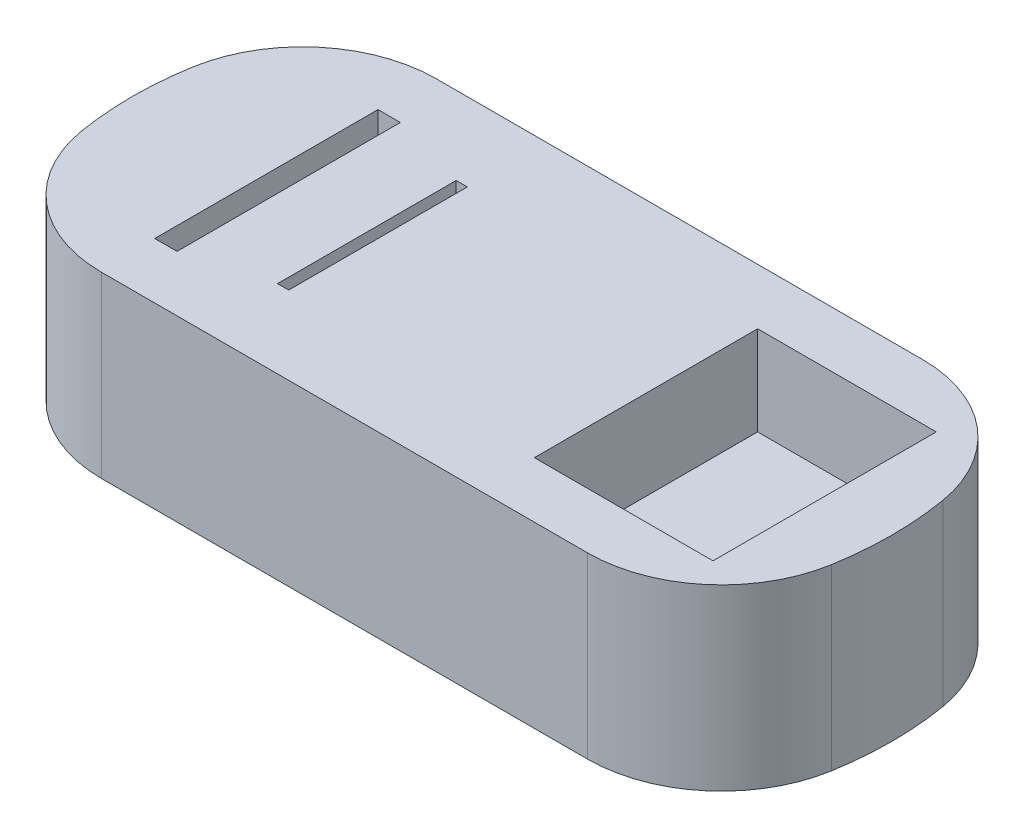
SolidWorks part; units mm, degrees
ref_plane "Alzado" through (0, 0, 0) normal (0, 0, 1) x (1, 0, 0)
ref_plane "Planta" through (0, 0, 0) normal (0, 1, 0) x (1, 0, 0)
ref_plane "Vista lateral" through (0, 0, 0) normal (1, 0, 0) x (0, 0, -1)
sketch "Croquis1" plane through (0, 0, 0) normal (0, 1, 0) x (1, 0, 0)
  line L1 (-150, -75) -> (150, -75)
  line L3 (-150, 75) -> (150, 75)
  line L5 (-150, -75) -> (150, 75) construction
  line L6 (-150, 75) -> (150, -75) construction
  arc A0 (-150, 75) -> (-150, -75) centre (-20.0962, 0) ccw
  arc A1 (150, 75) -> (150, -75) centre (20.0962, 0) cw
  point P0 (0, 0)
  point P8 (-170.0962, 0)
  point P9 (170.0962, 0)
  dimension "D3" = 150
  dimension "D4" = 150
  dimension "D1" = 300
  dimension "D2" = 150
extrude "Saliente-Extruir1" add sketch "Croquis1" along normal blind 80
fillet "Redondeo1" radius 60 4 edges at (-150, 40, -75) (150, 40, -75) (150, 40, 75) (-150, 40, 75)
sketch "Croquis2" plane through (0, 80, 0) normal (0, 1, 0) x (1, 0, 0)
  line L0 (-108.8374, -75) -> (108.8374, -75) construction
  line L1 (-110, 50) -> (-100, 50)
  line L2 (-110, 50) -> (-110, -50)
  line L3 (-110, -50) -> (-100, -50)
  line L4 (-100, 50) -> (-100, -50)
  point P5 (-105, -50)
  dimension "D1" = 10
  dimension "D2" = 100
  dimension "D3" = 25
  dimension "D4" = 100
extrude "Cortar-Extruir1" cut sketch "Croquis2" against normal blind 20 contours L2 L1 L4 L3
sketch "Croquis3" plane through (0, 80, 0) normal (0, 1, 0) x (1, 0, 0)
  line L0 (-100, 50) -> (-100, -50) construction
  line L1 (-65, 40) -> (-60, 40)
  line L2 (-65, 40) -> (-65, -40)
  line L3 (-65, -40) -> (-60, -40)
  line L4 (-60, 40) -> (-60, -40)
  line L5 (-108.8374, -75) -> (108.8374, -75) construction
  dimension "D1" = 5
  dimension "D2" = 80
  dimension "D3" = 35
  dimension "D4" = 35
extrude "Cortar-Extruir2" cut sketch "Croquis3" against normal blind 40
sketch "Croquis4" plane through (0, 80, 0) normal (0, 1, 0) x (1, 0, 0)
  line L0 (-108.8374, -75) -> (108.8374, -75) construction
  line L1 (60, 50) -> (140, 50)
  line L2 (60, 50) -> (60, -50)
  line L3 (60, -50) -> (140, -50)
  line L4 (140, 50) -> (140, -50)
  dimension "D1" = 80
  dimension "D2" = 100
  dimension "D3" = 25
  dimension "D4" = 60
extrude "Cortar-Extruir3" cut sketch "Croquis4" against normal blind 40 contours L2 L1 L4 L3
sketch "Croquis9" plane through (0, 0, 75) normal (0, 0, 1) x (1, 0, 0)
  line L0 (-474.8737, 162.2719) -> (-36.8737, 162.2719) construction
